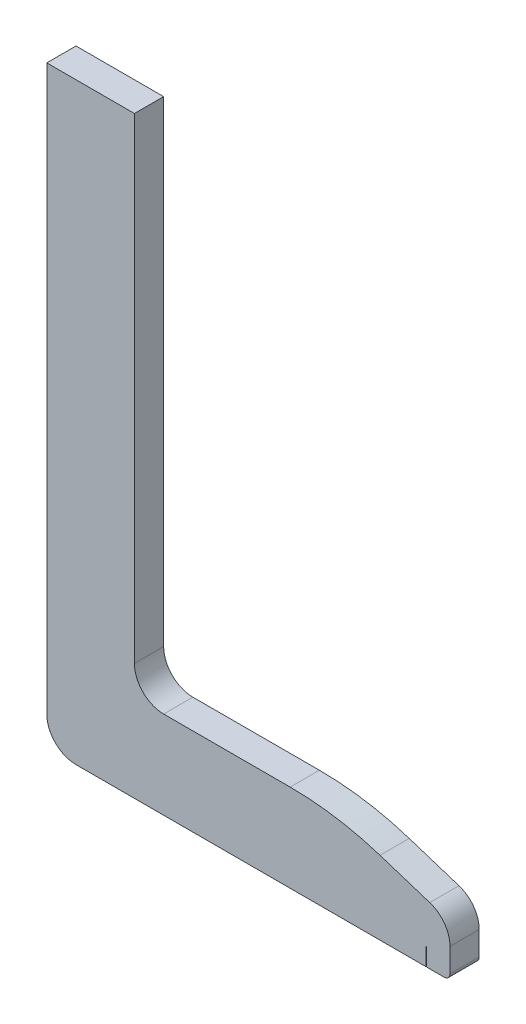
SolidWorks part; units mm, degrees
ref_plane "Front Plane" through (0, 0, 0) normal (0, 0, 1) x (1, 0, 0)
ref_plane "Top Plane" through (0, 0, 0) normal (0, 1, 0) x (1, 0, 0)
ref_plane "Right Plane" through (0, 0, 0) normal (1, 0, 0) x (0, 0, -1)
sketch "Sketch1" plane through (0, 0, 0) normal (0, 0, 1) x (1, 0, 0)
  line L0 (0, -1) -> (0, -96.5)
  line L1 (5, -101.5) -> (68, -101.5)
  line L2 (69, -100.5) -> (69, -96.43)
  line L3 (41.65, -86.5) -> (20, -86.5)
  line L4 (15, -81.5) -> (15, -61)
  line L6 (15, -61) -> (15, 0)
  line L8 (0, -1) -> (0, 0)
  line L10 (65.5369, -91.6721) -> (57.0187, -88.9206)
  line L19 (0, 0) -> (15, 0)
  arc A2 (69, -100.5) -> (68, -101.5) centre (68, -100.5) cw
  arc A4 (5, -101.5) -> (0, -96.5) centre (5, -96.5) cw
  arc A5 (15, -81.5) -> (20, -86.5) centre (20, -81.5) ccw
  arc A6 (65.5369, -91.6721) -> (69, -96.43) centre (64, -96.43) cw
  arc A7 (41.65, -86.5) -> (57.0187, -88.9206) centre (41.65, -136.5) cw
  point P9 (0, 0)
  point P12 (15, 0)
  point P15 (69, -101.5)
  point P18 (69, -86.5)
  point P21 (0, -101.5)
  point P24 (15, -86.5)
  dimension "D6" = 5
  dimension "D5" = 5
  dimension "D7" = 50
  dimension "D1" = 86.5
  dimension "D2" = 15
  dimension "D3" = 69
  dimension "D4" = 15
extrude "Boss-Extrude1" add sketch "Sketch1" along normal blind 5
sketch "Sketch2" plane through (0, -101.5, 0) normal (0, -1, 0) x (1, 0, 0)
  line L0 (0, 2.5) -> (64.9, 2.5) construction
  line L1 (0, 5) -> (0, 0) construction
  line L2 (5, 5) -> (68, 5) construction
  line L3 (64.85, 0) -> (64.95, 0)
  line L4 (64.85, 0) -> (64.85, 5)
  line L5 (64.85, 5) -> (64.95, 5)
  line L6 (64.95, 0) -> (64.95, 5)
  line L7 (64.85, 0) -> (64.95, 5) construction
  line L8 (64.85, 5) -> (64.95, 0) construction
  dimension "D1" = 64.9
  dimension "D2" = 0.1
extrude "Cut-Extrude2" cut sketch "Sketch2" against normal blind 3
equation "\"A.L\"= 0.07m"
equation "\"A.h\"= 0.007m"
equation "\"A.d\"= 0.005m"
equation "\"A.delta\"= 45.0001"
equation "\"A.w\"= 0m"
equation "\"A.v\"= 0.013m"
equation "\"A.s\"= 0.014m"
equation "\"A.t\"= 0.007m"
equation "\"B.L\"= 0.065m"
equation "\"B.h\"= 0.008m"
equation "\"B.s\"= 0.016m"
equation "\"B.t\"= 0.008m"
equation "\"C.h\"= 0.0065m"
equation "\"C.d\"= 0.005m"
equation "\"C.L\"= 0.05m"
equation "\"C.wmax\"= 0.003m"
equation "\"D.L\"= 0.06m"
equation "\"D.h\"= 0.008m"
equation "\"D.s\"= 0.012m"
equation "\"D.t\"= 0.008m"
equation "\"a_h\"= 0.0001m"
equation "\"a_d\"= 0.005m"
equation "\"a_L\"= 0.008m"
equation "\"b_h\"= 0.0004m"
equation "\"b_d\"= 0.005m"
equation "\"b_L\"= 0.007m"
equation "\"c_h\"= 0.0001m"
equation "\"c_d\"= 0.005m"
equation "\"c_L\"= 0.01m"
equation "\"d_h\"= 0.0001m"
equation "\"d_d\"= 0.005m"
equation "\"d_L\"= 0.01m"
equation "\"S.h\"= 0.015m"
equation "\"S.L\"= 0.09275m"
equation "\"D1@Sketch1\"=\"S.L\"-\"C.wmax\"-\"C.h\"/2"
equation "\"D2@Sketch1\"=\"S.h\""
equation "\"D3@Sketch1\"=\"C.L\"+\"S.h\"+0.004"
equation "\"D4@Sketch1\"=\"S.h\""
equation "\"D1@Boss-Extrude1\"=0.005m"
equation "\"D1@Sketch2\"=\"C.L\"+\"S.h\"-\"d_h\""
equation "\"D2@Sketch2\"=\"d_h\""
